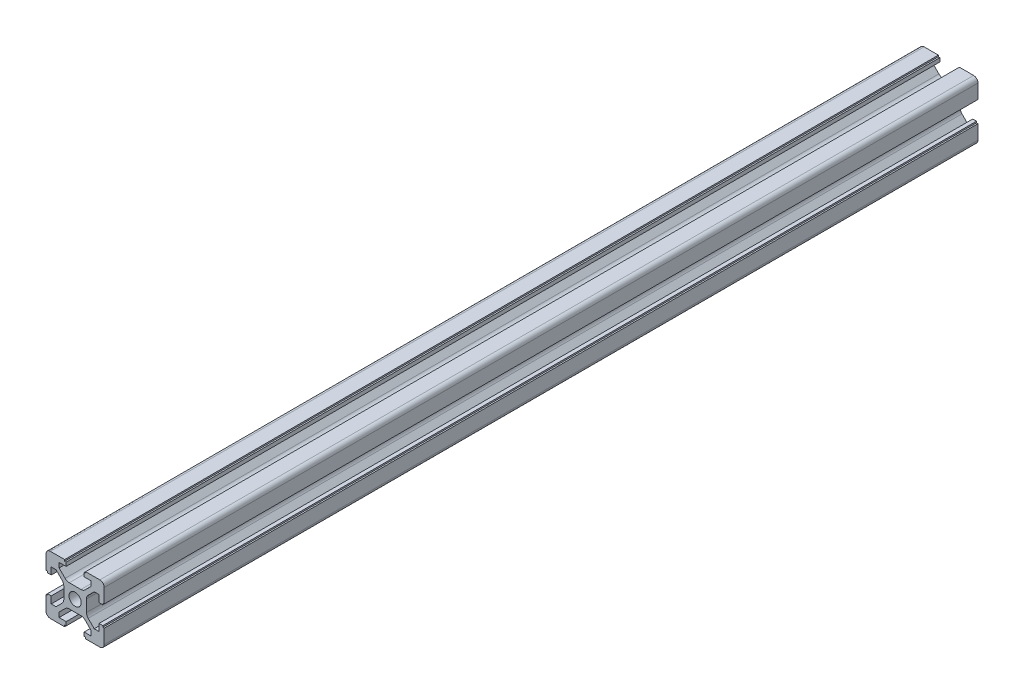
SolidWorks part; units mm, degrees
material "6061 合金"
ref_plane "前视基准面" through (0, 0, 0) normal (0, 0, 1) x (1, 0, 0)
ref_plane "上视基准面" through (0, 0, 0) normal (0, 1, 0) x (1, 0, 0)
ref_plane "右视基准面" through (0, 0, 0) normal (1, 0, 0) x (0, 0, -1)
sketch "草图1" plane through (0, 0, 0) normal (0, 0, 1) x (1, 0, 0)
  line L0 (-3.4251, 4.4858) -> (-5.5, 6.5607)
  line L6 (-5.5, 6.5607) -> (-5.5, 8.2)
  line L7 (-5.5, 8.2) -> (-3.1, 8.2)
  line L22 (-3.1, 8.2) -> (-3.1, 9.5)
  line L41 (-3.6, 10) -> (-8.5, 10)
  line L42 (0, 0) -> (-29.7212, 29.7212) construction
  line L43 (0, -8.5755) -> (0, 20.7623) construction
  line L44 (-10, 3.6) -> (-10, 8.5)
  line L46 (-8.2, 5.5) -> (-8.2, 3.1)
  line L47 (-6.5607, 5.5) -> (-8.2, 5.5)
  line L48 (-4.4858, 3.4251) -> (-6.5607, 5.5)
  line L49 (4.4858, 3.4251) -> (6.5607, 5.5)
  line L50 (6.5607, 5.5) -> (8.2, 5.5)
  line L51 (8.2, 5.5) -> (8.2, 3.1)
  line L53 (10, 3.6) -> (10, 8.5)
  line L54 (3.6, 10) -> (8.5, 10)
  line L56 (5.5, 8.2) -> (3.1, 8.2)
  line L57 (5.5, 6.5607) -> (5.5, 8.2)
  line L58 (3.4251, 4.4858) -> (5.5, 6.5607)
  line L59 (11, 0) -> (-11, 0) construction
  line L60 (3.4251, -4.4858) -> (5.5, -6.5607)
  line L61 (5.5, -6.5607) -> (5.5, -8.2)
  line L62 (5.5, -8.2) -> (3.1, -8.2)
  line L64 (3.6, -10) -> (8.5, -10)
  line L65 (10, -3.6) -> (10, -8.5)
  line L67 (8.2, -5.5) -> (8.2, -3.1)
  line L68 (6.5607, -5.5) -> (8.2, -5.5)
  line L69 (4.4858, -3.4251) -> (6.5607, -5.5)
  line L70 (-4.4858, -3.4251) -> (-6.5607, -5.5)
  line L71 (-6.5607, -5.5) -> (-8.2, -5.5)
  line L72 (-8.2, -5.5) -> (-8.2, -3.1)
  line L74 (-10, -3.6) -> (-10, -8.5)
  line L75 (-3.6, -10) -> (-8.5, -10)
  line L77 (-5.5, -8.2) -> (-3.1, -8.2)
  line L78 (-5.5, -6.5607) -> (-5.5, -8.2)
  line L79 (-3.4251, -4.4858) -> (-5.5, -6.5607)
  line L80 (-3.9, -2.0109) -> (-3.9, 2.0109)
  line L81 (-2.0109, 3.9) -> (2.0109, 3.9)
  line L82 (3.9, 2.0109) -> (3.9, -2.0109)
  line L83 (2.0109, -3.9) -> (-2.0109, -3.9)
  line L84 (-3.1, 9.5) -> (-3.6, 9.5)
  line L85 (-3.6, 9.5) -> (-3.6, 10)
  line L86 (3.6, 9.5) -> (3.6, 10)
  line L87 (3.1, 9.5) -> (3.6, 9.5)
  line L88 (3.1, 8.2) -> (3.1, 9.5)
  line L89 (-9.5, 3.1) -> (-9.5, 3.6)
  line L90 (-9.5, 3.6) -> (-10, 3.6)
  line L91 (-8.2, 3.1) -> (-9.5, 3.1)
  line L92 (8.2, 3.1) -> (9.5, 3.1)
  line L93 (9.5, 3.6) -> (10, 3.6)
  line L94 (9.5, 3.1) -> (9.5, 3.6)
  line L95 (9.5, -3.1) -> (9.5, -3.6)
  line L96 (9.5, -3.6) -> (10, -3.6)
  line L97 (8.2, -3.1) -> (9.5, -3.1)
  line L98 (3.1, -8.2) -> (3.1, -9.5)
  line L99 (3.1, -9.5) -> (3.6, -9.5)
  line L100 (3.6, -9.5) -> (3.6, -10)
  line L101 (-3.6, -9.5) -> (-3.6, -10)
  line L102 (-3.1, -9.5) -> (-3.6, -9.5)
  line L103 (-3.1, -8.2) -> (-3.1, -9.5)
  line L104 (-8.2, -3.1) -> (-9.5, -3.1)
  line L105 (-9.5, -3.6) -> (-10, -3.6)
  line L106 (-9.5, -3.1) -> (-9.5, -3.6)
  circle A0 centre (0, 0) radius 2.1
  arc A1 (-10, -8.5) -> (-8.5, -10) centre (-8.5, -8.5) ccw
  arc A2 (8.5, -10) -> (10, -8.5) centre (8.5, -8.5) ccw
  arc A3 (10, 8.5) -> (8.5, 10) centre (8.5, 8.5) ccw
  arc A4 (-8.5, 10) -> (-10, 8.5) centre (-8.5, 8.5) ccw
  arc A5 (-4.4858, 3.4251) -> (-3.9, 2.0109) centre (-5.9, 2.0109) cw
  arc A6 (-3.4251, 4.4858) -> (-2.0109, 3.9) centre (-2.0109, 5.9) ccw
  arc A7 (3.4251, 4.4858) -> (2.0109, 3.9) centre (2.0109, 5.9) cw
  arc A8 (4.4858, 3.4251) -> (3.9, 2.0109) centre (5.9, 2.0109) ccw
  arc A9 (4.4858, -3.4251) -> (3.9, -2.0109) centre (5.9, -2.0109) cw
  arc A10 (-4.4858, -3.4251) -> (-3.9, -2.0109) centre (-5.9, -2.0109) ccw
  arc A11 (3.4251, -4.4858) -> (2.0109, -3.9) centre (2.0109, -5.9) ccw
  arc A12 (-3.4251, -4.4858) -> (-2.0109, -3.9) centre (-2.0109, -5.9) cw
  point P74 (-10, -10)
  point P77 (10, -10)
  point P80 (10, 10)
  point P83 (-10, 10)
  point P86 (-3.9, 2.8393)
  point P89 (-2.8393, 3.9)
  point P92 (2.8393, 3.9)
  point P95 (3.9, 2.8393)
  point P98 (3.9, -2.8393)
  point P101 (-3.9, -2.8393)
  point P104 (2.8393, -3.9)
  point P107 (-2.8393, -3.9)
  dimension "D8" = 4.2
  dimension "D7" = 1.5
  dimension "D12" = 2
  dimension "D1" = 45
  dimension "D2" = 20
  dimension "D3" = 0.5
  dimension "D4" = 6.2
  dimension "D5" = 11
  dimension "D6" = 1.5
  dimension "D9" = 0.5
  dimension "D10" = 1.8
  dimension "D11" = 6.1
extrude "凸台-拉伸1" add sketch "草图1" along normal mid plane 300
